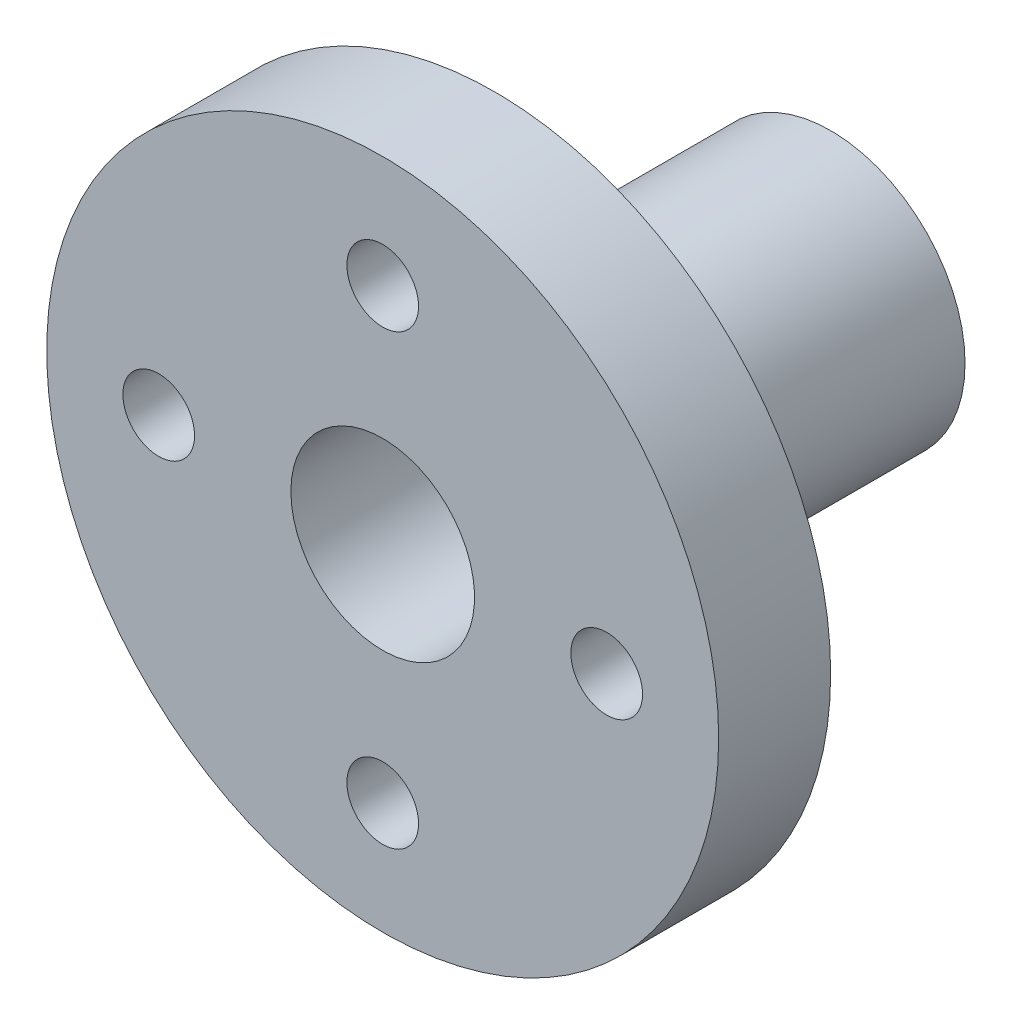
SolidWorks part; units mm, degrees
ref_plane "前视基准面" through (0, 0, 0) normal (0, 0, 1) x (1, 0, 0)
ref_plane "上视基准面" through (0, 0, 0) normal (0, 1, 0) x (1, 0, 0)
ref_plane "右视基准面" through (0, 0, 0) normal (1, 0, 0) x (0, 0, -1)
other "Configuration Table"
sketch "草图1" plane through (0, 0, 0) normal (0, 0, 1) x (1, 0, 0)
  line L0 (-1.894, 14.3116) -> (-1.894, 4.3116) construction
  line L1 (-1.894, 4.3116) -> (-1.894, -5.6884) construction
  line L2 (-11.894, 4.3116) -> (-1.894, 4.3116) construction
  line L3 (-1.894, 4.3116) -> (8.106, 4.3116) construction
  circle A0 centre (-1.894, 4.3116) radius 10 construction
  circle A1 centre (-1.894, 14.3116) radius 1.6
  circle A2 centre (8.106, 4.3116) radius 1.6
  circle A3 centre (-1.894, -5.6884) radius 1.6
  circle A4 centre (-11.894, 4.3116) radius 1.6
  circle A5 centre (-1.894, 4.3116) radius 15
  dimension "D1" = 20
  dimension "D2" = 3.2
  dimension "D3" = 30
extrude "凸台-拉伸1" add sketch "草图1" along normal blind 5
sketch "草图2" plane through (0, 0, 0) normal (0, 0, 1) x (1, 0, 0)
  circle A0 centre (-1.894, 4.3116) radius 6
  dimension "D1" = 12
extrude "凸台-拉伸2" add sketch "草图2" against normal blind 15
sketch "草图3" plane through (0, 0, -15) normal (0, 0, -1) x (-1, 0, 0)
  circle A0 centre (1.894, 4.3116) radius 4.1
  dimension "D1" = 8.2
extrude "切除-拉伸1" cut sketch "草图3" against normal through all
sketch "草图4" plane through (0, 0, 0) normal (0, 1, 0) x (1, 0, 0)
  line L0 (-1.894, 15) -> (-1.894, 0) construction
  line L1 (2.206, 15) -> (-5.994, 15) construction
  line L2 (13.106, 0) -> (-16.894, 0) construction
  circle A0 centre (-1.894, 5.299) radius 1.6
  dimension "D1" = 3.2
extrude "切除-拉伸2" cut sketch "草图4" along normal mid plane 30 contours A0
